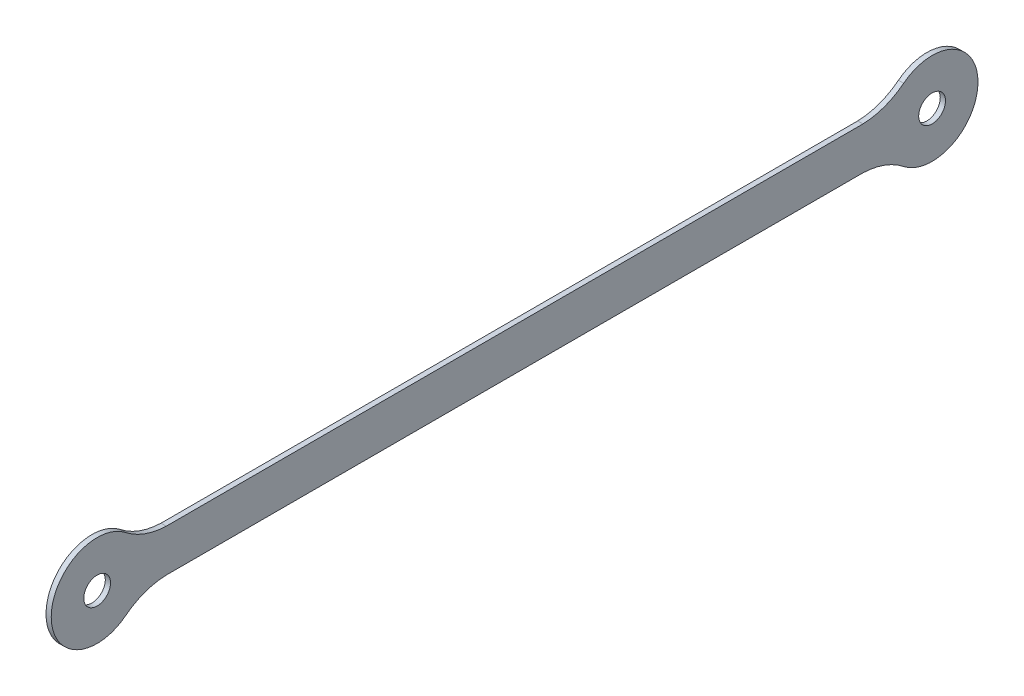
SolidWorks part; units mm, degrees
ref_plane "前基準面" through (0, 0, 0) normal (0, 0, 1) x (1, 0, 0)
ref_plane "上基準面" through (0, 0, 0) normal (0, 1, 0) x (1, 0, 0)
ref_plane "右基準面" through (0, 0, 0) normal (1, 0, 0) x (0, 0, -1)
sketch "草圖2" plane through (0, 0, 0) normal (1, 0, 0) x (0, 0, -1)
  line L1 (-86.2161, 6.0903) -> (114.0386, 6.0903)
  line L2 (-106.0888, 0) -> (106.0888, 0) construction
  line L3 (114.0386, -6.0903) -> (-86.2161, -6.0903)
  line L4 (-106.0888, 0) -> (133.9112, 0) construction
  arc A0 (125.7362, -10.3584) -> (114.0386, -6.0903) centre (113.41, -25.9766) ccw
  arc A1 (-97.9137, 10.3584) -> (-97.9137, -10.3584) centre (-106.0888, 0) ccw
  arc A3 (125.7362, 10.3584) -> (114.0386, 6.0903) centre (113.41, 25.9766) cw
  arc A4 (-97.9137, 10.3584) -> (-86.2161, 6.0903) centre (-85.5875, 25.9766) ccw
  arc A5 (-97.9137, -10.3584) -> (-86.2161, -6.0903) centre (-85.5875, -25.9766) cw
  arc A7 (125.7362, 10.3584) -> (125.7362, -10.3584) centre (133.9112, 0) cw
  circle A8 centre (133.9112, 0) radius 3.85
  circle A9 centre (-106.0888, 0) radius 3.85
  dimension "D2" = 12.1806
  dimension "D1" = 240
extrude "填料-伸長1" add sketch "草圖2" along normal blind 1.5
